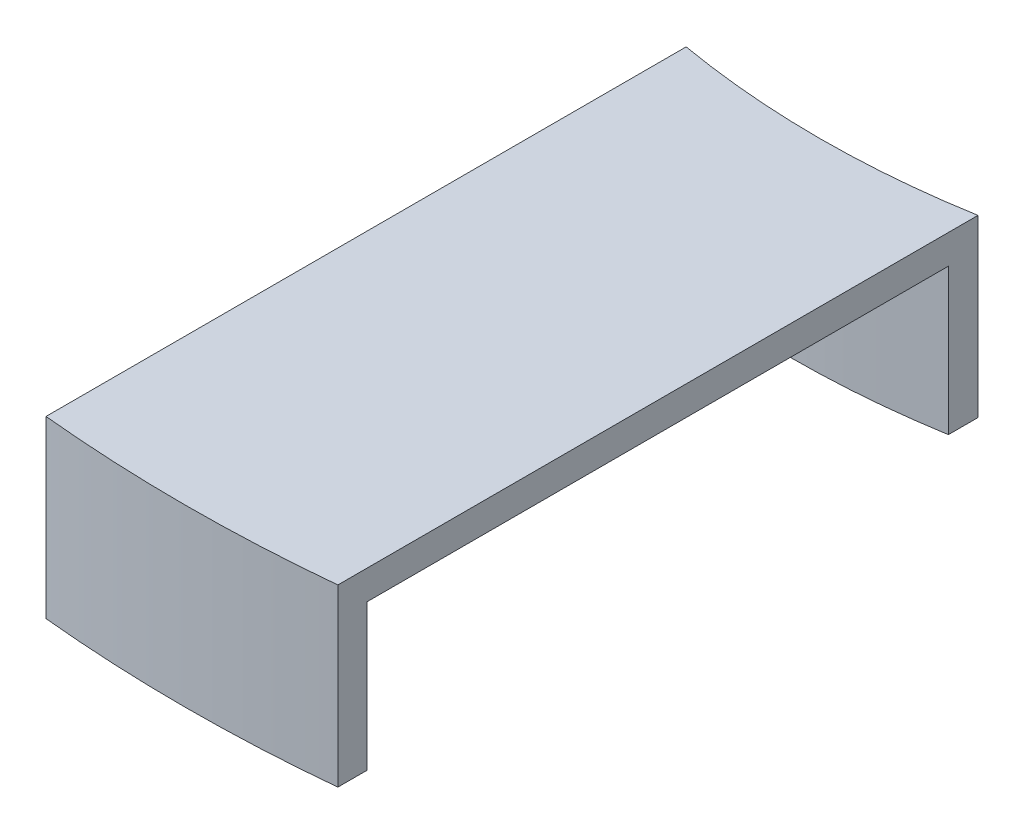
SolidWorks part; units mm, degrees
ref_plane "Front Plane" through (0, 0, 0) normal (0, 0, 1) x (1, 0, 0)
ref_plane "Top Plane" through (0, 0, 0) normal (0, 1, 0) x (1, 0, 0)
ref_plane "Right Plane" through (0, 0, 0) normal (1, 0, 0) x (0, 0, -1)
sketch "Sketch1" plane through (0, 0, 0) normal (0, 1, 0) x (1, 0, 0)
  line L1 (5, -100.038) -> (-5, -100.038)
  line L2 (5, -100.038) -> (5, -0.038)
  line L3 (5, -0.038) -> (-5, -0.038)
  line L4 (-5, -100.038) -> (-5, -0.038)
  line L5 (5, -100.038) -> (-5, -0.038) construction
  line L6 (5, -0.038) -> (-5, -100.038) construction
  circle A0 centre (0, 0) radius 30.2895
  circle A1 centre (0, 0) radius 50.038
  point P4 (0, -50.038)
  dimension "D1" = 100.076
  dimension "D2" = 60.579
  dimension "D3" = 10
  dimension "D4" = 100
extrude "Boss-Extrude1" add sketch "Sketch1" along normal blind 5 contours L4 A1 L2 A0
shell "Shell2" thickness 1
